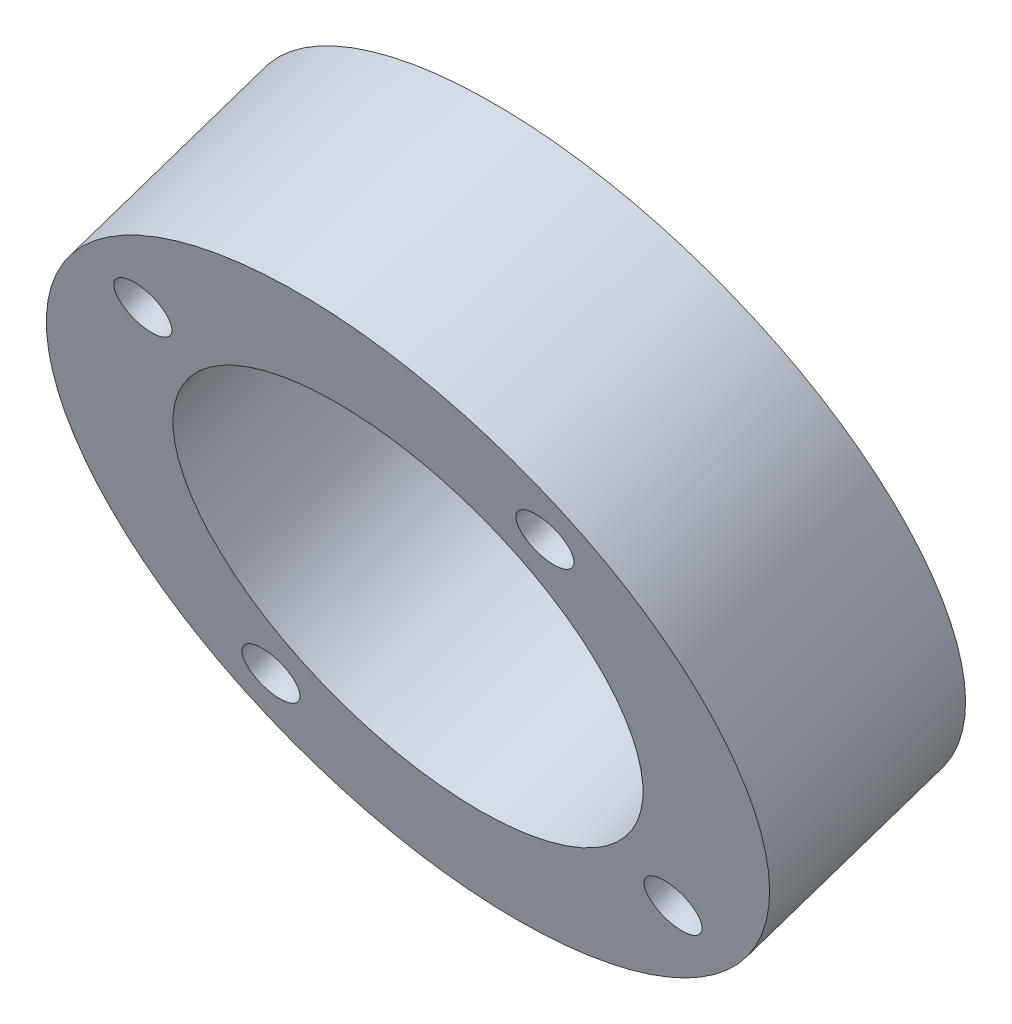
SolidWorks part; units mm, degrees
material "6061-T6 (SS)"
ref_plane "Front" through (0, 0, 0) normal (0, 0, 1) x (1, 0, 0)
ref_plane "Top" through (0, 0, 0) normal (0, 1, 0) x (1, 0, 0)
ref_plane "Right" through (0, 0, 0) normal (1, 0, 0) x (0, 0, -1)
sketch "Sketch1" plane through (0, -336.5004, 1001.0435) normal (0, -0.3186, 0.9479) x (1, 0, 0)
  circle A0 centre (0, 892.2529) radius 31.75
  circle A1 centre (0, 892.2529) radius 20.6375
  dimension "D1" = 63.5
  dimension "D2" = 41.275
extrude "Boss-Extrude1" add sketch "Sketch1" along normal up to surface (19.05 mm away)
hole_wizard "1/4-20 Tapped Hole1" positions "Sketch2" profile "Sketch3" tap size "1/4-20" standard "ANSI Inch" end condition through all
sketch "Sketch2" plane through (0, -336.5004, 1001.0435) normal (0, 0.3186, -0.9479) x (-1, 0, 0)
  line L0 (-18.5218, 910.7747) -> (18.5218, 910.7747) construction
  line L1 (18.5218, 910.7747) -> (18.5218, 873.7311) construction
  line L2 (18.5218, 873.7311) -> (-18.5218, 873.7311) construction
  line L3 (-18.5218, 873.7311) -> (-18.5218, 910.7747) construction
  circle A0 centre (0, 892.2529) radius 26.1938
  point P0 (18.5218, 910.7747)
  point P2 (-18.5218, 910.7747)
  point P4 (-18.5218, 873.7311)
  point P6 (18.5218, 873.7311)
  dimension "D1" = 52.3875
sketch "Sketch3" plane through (-18.5218, 526.8041, 1291.243) normal (1, 0, 0) x (0, 0.9479, 0.3186)
  line L0 (0, 0) -> (0, 38.2284)
  line L1 (0, 38.2284) -> (2.5527, 38.2284)
  line L2 (2.5527, 38.2284) -> (2.5527, 0)
  line L5 (2.5527, 0) -> (0, 0)
  line L11 (0, -6.35) -> (0, 107.95) construction
  dimension "Thru Tap Drill Dia." = 5.1054
  dimension "Thru Tap Drill Depth" = 38.2284
cosmetic thread "Hole Thread1" parameters "D2"=6.35
cosmetic thread "Hole Thread2" parameters "D2"=6.35
cosmetic thread "Hole Thread3" parameters "D2"=6.35
cosmetic thread "Hole Thread4" parameters "D2"=6.35
